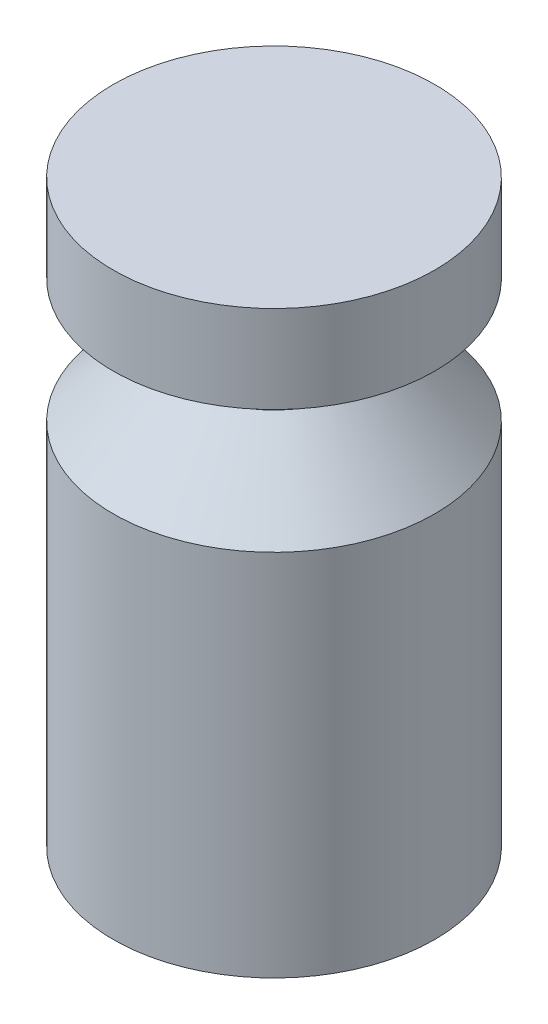
SolidWorks part; units mm, degrees
ref_plane "Front Plane" through (0, 0, 0) normal (0, 0, 1) x (1, 0, 0)
ref_plane "Top Plane" through (0, 0, 0) normal (0, 1, 0) x (1, 0, 0)
ref_plane "Right Plane" through (0, 0, 0) normal (1, 0, 0) x (0, 0, -1)
sketch "Sketch1" plane through (0, 0, 0) normal (0, 0, 1) x (1, 0, 0)
  line L0 (0, 0) -> (14.6978, 0)
  line L1 (14.6978, 0) -> (14.6978, 33.7)
  line L2 (14.6978, 33.7) -> (8.25, 40.4)
  line L3 (8.25, 40.4) -> (8.25, 45)
  line L4 (8.25, 45) -> (14.6978, 45)
  line L5 (14.6978, 45) -> (14.6978, 53)
  line L6 (14.6978, 53) -> (0, 53)
  line L7 (0, 53) -> (0, 0)
  dimension "D1" = 53
  dimension "D2" = 8
  dimension "D3" = 4.6
  dimension "D4" = 8.25
  dimension "D5" = 14.6978
  dimension "D6" = 6.7
revolve "Revolve1" add sketch "Sketch1" angle 360 about L7
